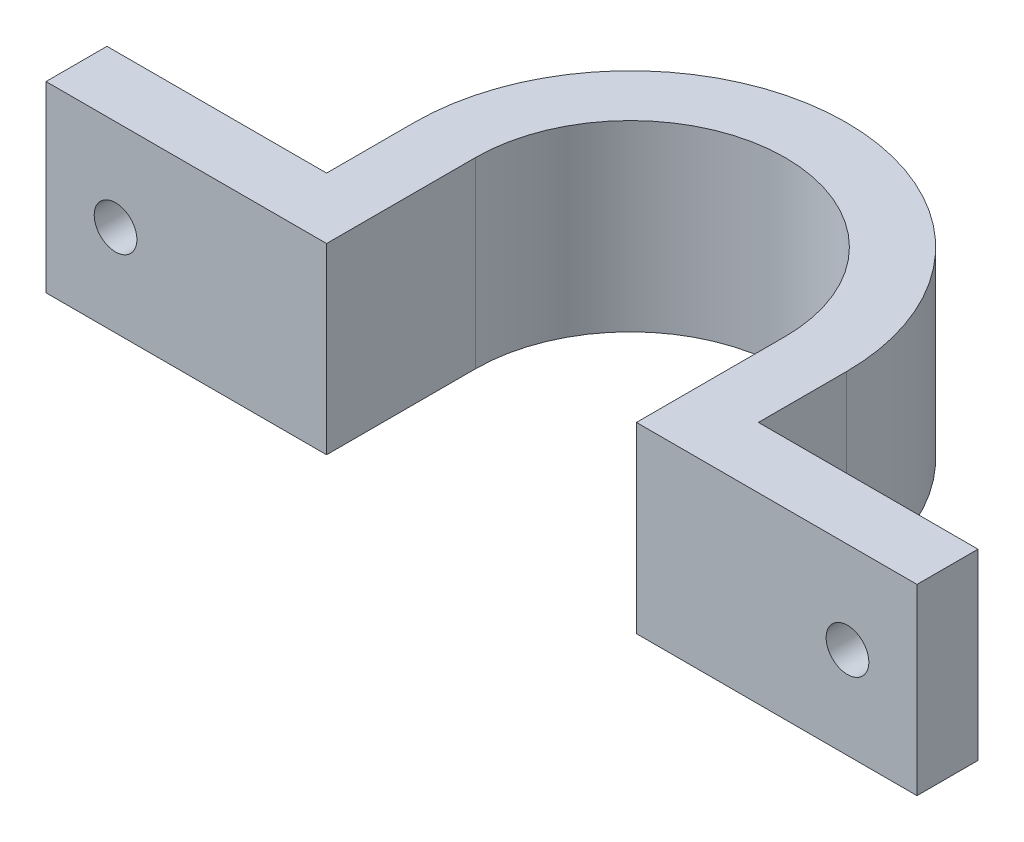
SolidWorks part; units mm, degrees
ref_plane "Front Plane" through (0, 0, 0) normal (0, 0, 1) x (1, 0, 0)
ref_plane "Top Plane" through (0, 0, 0) normal (0, 1, 0) x (1, 0, 0)
ref_plane "Right Plane" through (0, 0, 0) normal (1, 0, 0) x (0, 0, -1)
sketch "Sketch1" plane through (0, 0, 0) normal (0, 1, 0) x (1, 0, 0)
  line L6 (-35.7, -7.2) -> (-35.7, -12.2)
  line L7 (-35.7, -12.2) -> (-12.7, -12.2)
  line L8 (-12.7, -12.2) -> (-12.7, 0)
  line L10 (35.7, -7.2) -> (35.7, -12.2)
  line L11 (35.7, -12.2) -> (12.7, -12.2)
  line L12 (12.7, -12.2) -> (12.7, 0)
  line L14 (-17.7, 0) -> (-17.7, -7.2)
  line L15 (-17.7, -7.2) -> (-35.7, -7.2)
  line L16 (17.7, 0) -> (17.7, -7.2)
  line L17 (17.7, -7.2) -> (35.7, -7.2)
  arc A0 (17.7, 0) -> (-17.7, 0) centre (0, 0) ccw
  arc A1 (-12.7, 0) -> (12.7, 0) centre (0, 0) cw
  point P12 (0, -12.7)
  dimension "D1" = 12.7
  dimension "D2" = 5
  dimension "D5" = 0.5
  dimension "D3" = 5
  dimension "D4" = 18
extrude "Boss-Extrude1" add sketch "Sketch1" along normal blind 15
sketch "Sketch2" plane through (0, 0, 7.2) normal (0, 0, -1) x (-1, 0, 0)
  line L0 (-35.7, 7.5) -> (-30, 7.5) construction
  line L2 (35.7, 7.5) -> (30, 7.5) construction
  line L4 (-35.7, 15) -> (-35.7, 0) construction
  line L5 (35.7, 15) -> (35.7, 0) construction
  circle A0 centre (-30, 7.5) radius 1.75
  circle A1 centre (30, 7.5) radius 1.75
  dimension "D1" = 3.5
  dimension "D2" = 60
extrude "Cut-Extrude1" cut sketch "Sketch2" against normal through all
